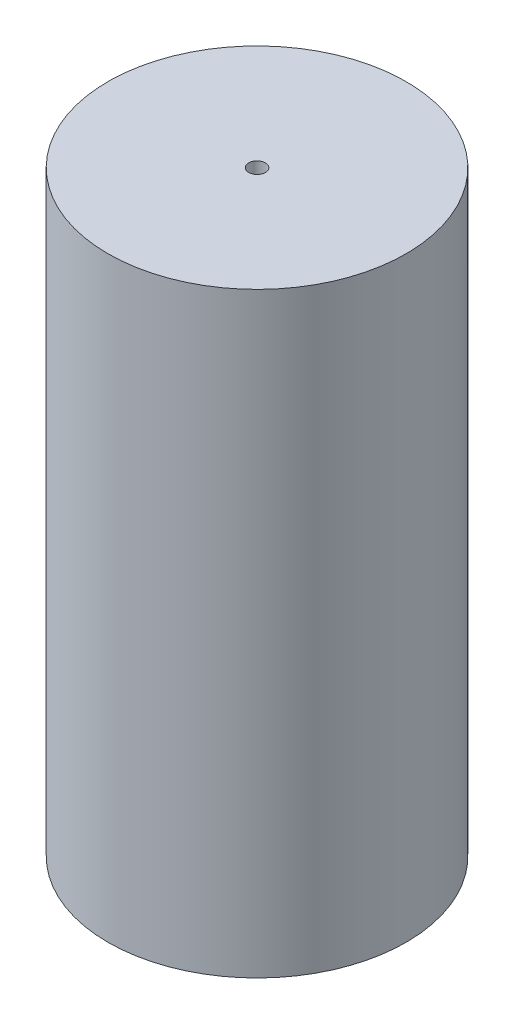
SolidWorks part; units mm, degrees
ref_plane "Front Plane" through (0, 0, 0) normal (0, 0, 1) x (1, 0, 0)
ref_plane "Top Plane" through (0, 0, 0) normal (0, 1, 0) x (1, 0, 0)
ref_plane "Right Plane" through (0, 0, 0) normal (1, 0, 0) x (0, 0, -1)
sketch "Sketch1" plane through (0, 0, 0) normal (0, 1, 0) x (1, 0, 0)
  circle A0 centre (0, 0) radius 25
extrude "Boss-Extrude1" add sketch "Sketch1" along normal blind 100
sketch "Sketch3" plane through (0, 100, 0) normal (0, 1, 0) x (1, 0, 0)
  circle A0 centre (0, 0) radius 1.4
  point P3 (0, 0)
  point P4 (0, 0)
  point P5 (0, 0)
extrude "Cut-Extrude3" cut sketch "Sketch3" against normal blind 20
sketch "Sketch5" plane through (0, 0, 0) normal (0, -1, 0) x (1, 0, 0)
  circle A0 centre (0, 0) radius 1.4
extrude "Cut-Extrude4" cut sketch "Sketch5" against normal blind 20
